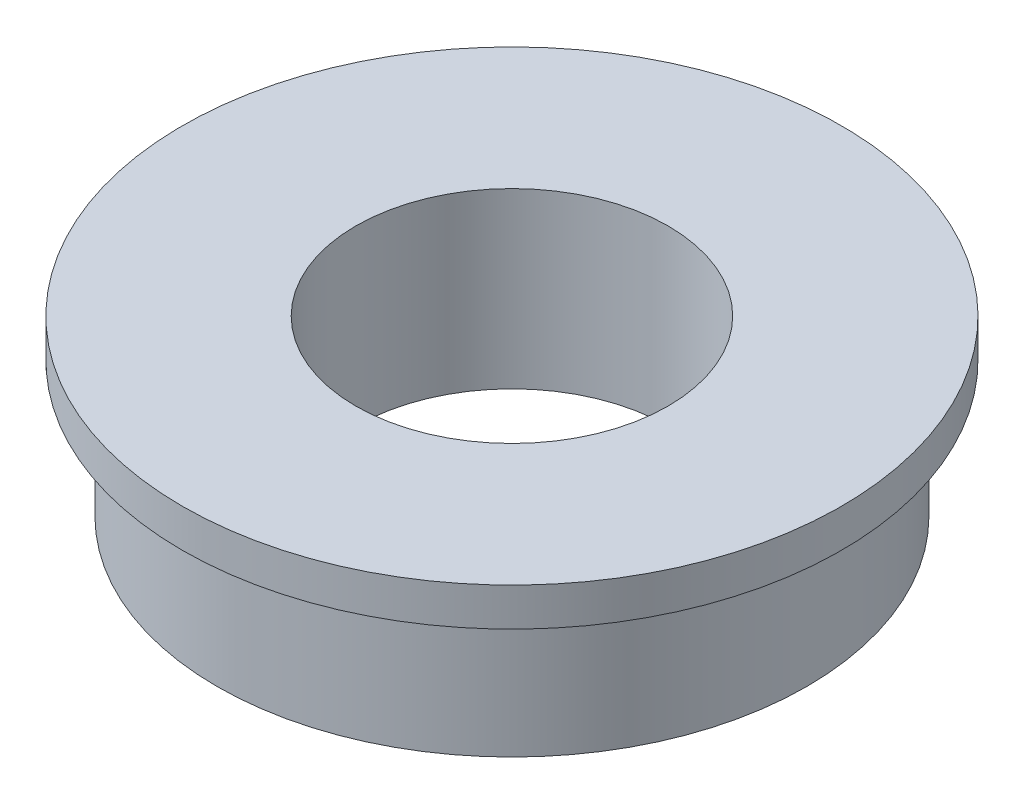
SolidWorks part; units mm, degrees
material "AISI 1020"
ref_plane "Front Plane" through (0, 0, 0) normal (0, 0, 1) x (1, 0, 0)
ref_plane "Top Plane" through (0, 0, 0) normal (0, 1, 0) x (1, 0, 0)
ref_plane "Right Plane" through (0, 0, 0) normal (1, 0, 0) x (0, 0, -1)
sketch "Sketch2" plane through (0, 0, 0) normal (0, 1, 0) x (1, 0, 0)
  circle A0 centre (0, 0) radius 4.5
  circle A1 centre (0, 0) radius 8.5
  dimension "D1" = 9
  dimension "D2" = 17
extrude "Boss-Extrude1" add sketch "Sketch2" along normal blind 5
sketch "Sketch3" plane through (0, 5, 0) normal (0, 1, 0) x (1, 0, 0)
  circle A0 centre (0, 0) radius 9.5
  circle A1 centre (0, 0) radius 8.5 construction
  circle A2 centre (0, 0) radius 8.5
  dimension "D1" = 1
extrude "Boss-Extrude2" add sketch "Sketch3" against normal blind 1.1
